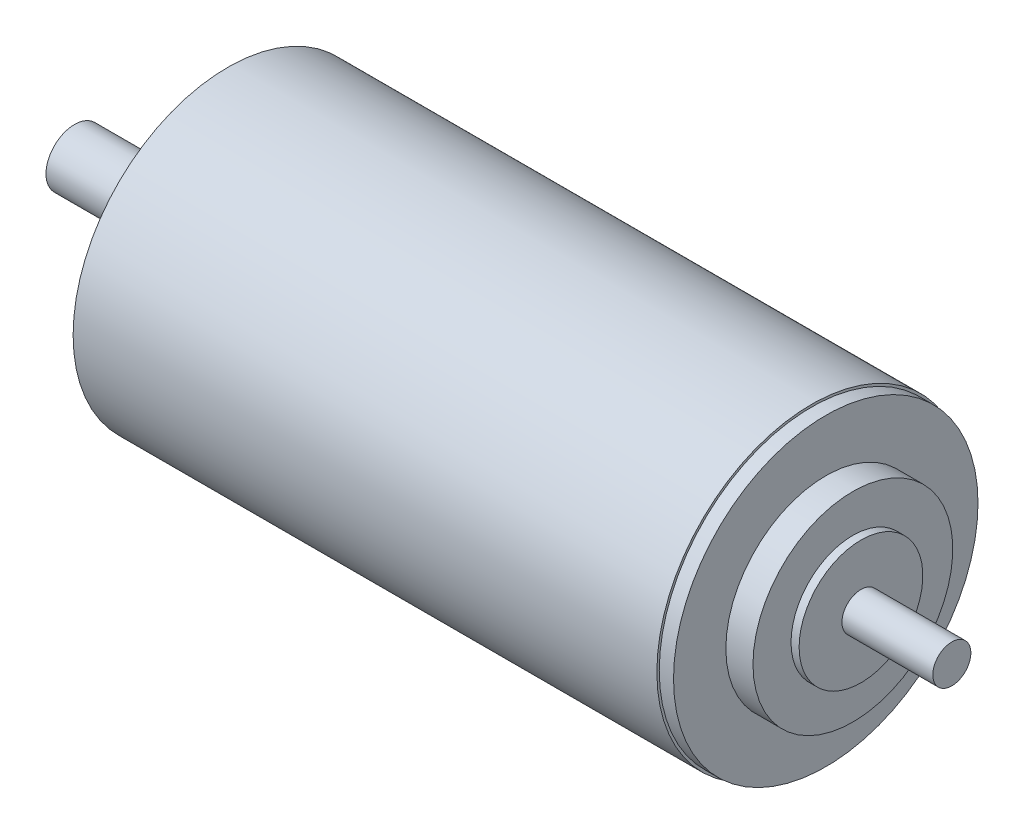
SolidWorks part; units mm, degrees
ref_plane "Plan de face" through (0, 0, 0) normal (0, 0, 1) x (1, 0, 0)
ref_plane "Plan de dessus" through (0, 0, 0) normal (0, 1, 0) x (1, 0, 0)
ref_plane "Plan de droite" through (0, 0, 0) normal (1, 0, 0) x (0, 0, -1)
sketch "Esquisse1" plane through (0, 0, 0) normal (0, 0, 1) x (1, 0, 0)
  line L0 (0, 0) -> (0, 6)
  line L1 (0, 6) -> (28.1, 6)
  line L2 (28.1, 6) -> (28.1, 18)
  line L3 (28.1, 18) -> (32.2, 18)
  line L4 (32.2, 18) -> (32.2, 32.5)
  line L5 (32.2, 32.5) -> (154.9, 32.5)
  line L6 (154.9, 32.5) -> (154.9, 32)
  line L7 (154.9, 32) -> (157.9, 32)
  line L8 (157.9, 32) -> (157.9, 21)
  line L9 (157.9, 21) -> (163.6, 21)
  line L10 (163.6, 21) -> (163.6, 13)
  line L11 (163.6, 13) -> (165.3, 13)
  line L12 (165.3, 13) -> (165.3, 4)
  line L13 (165.3, 4) -> (184.4, 4)
  line L14 (184.4, 4) -> (184.4, 0)
  line L15 (0, 0) -> (184.4, 0) construction
  line L16 (0, 0) -> (184.4, 0)
  dimension "D1" = 6
  dimension "D2" = 18
  dimension "D3" = 32.5
  dimension "D4" = 32.2
  dimension "D5" = 4.1
  dimension "D6" = 0.5
  dimension "D7" = 21
  dimension "D8" = 13
  dimension "D9" = 4
  dimension "D10" = 19.1
  dimension "D11" = 1.7
  dimension "D12" = 5.7
  dimension "D13" = 3
  dimension "D14" = 131.4
revolve "Révolution1" add sketch "Esquisse1" angle 360 about L15
